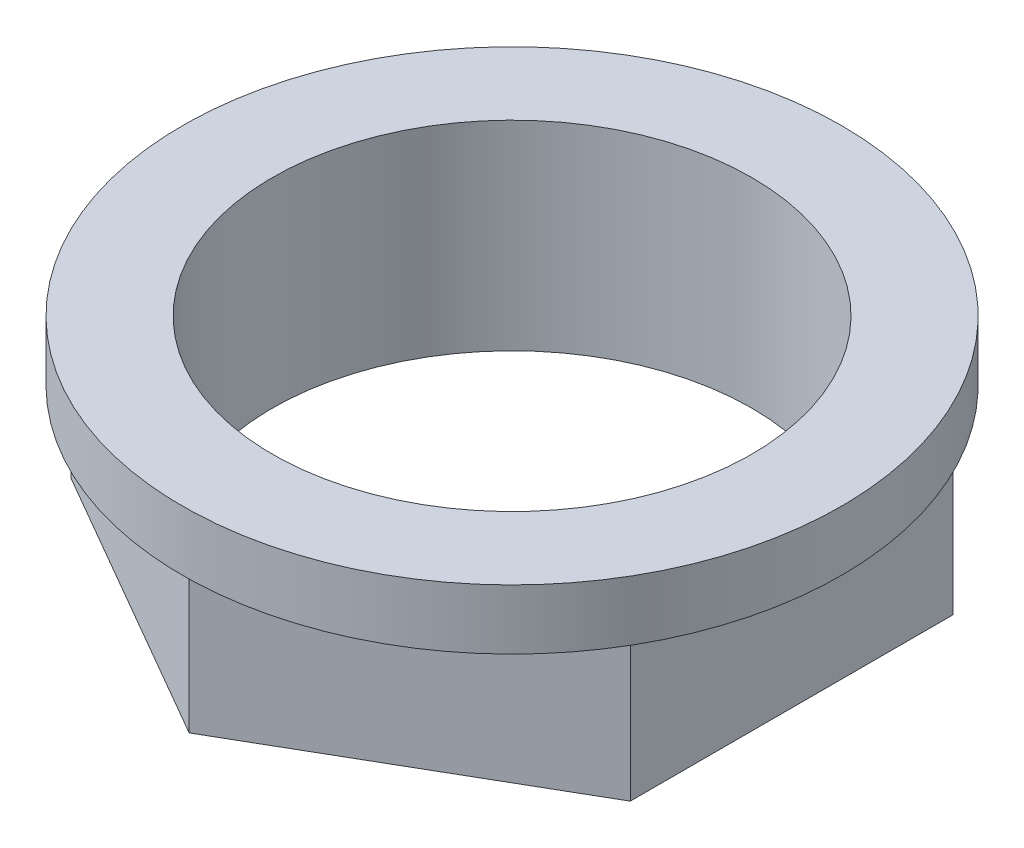
SolidWorks part; units mm, degrees
ref_plane "Спереди" through (0, 0, 0) normal (0, 0, 1) x (1, 0, 0)
ref_plane "Сверху" through (0, 0, 0) normal (0, 1, 0) x (1, 0, 0)
ref_plane "Справа" through (0, 0, 0) normal (1, 0, 0) x (0, 0, -1)
sketch "Sketch1" plane through (0, 0, 0) normal (0, 0, 1) x (1, 0, 0)
  line L0 (0, -3.4966) -> (0, 6.9158) construction
  line L2 (-8.25, 0) -> (-6, 0)
  line L3 (-8.25, 0) -> (-8.25, -5)
  line L4 (-8.25, -5) -> (-6, -5)
  line L5 (-6, 0) -> (-6, -5)
  dimension "D1" = 12
  dimension "D2" = 16.5
  dimension "D3" = 5
revolve "Revolve1" add sketch "Sketch1" angle 360 about L0
sketch "Sketch2" plane through (0, -5, 0) normal (0, -1, 0) x (1, 0, 0)
  line L1 (0, 8.0829) -> (-7, 4.0415)
  line L2 (-7, 4.0415) -> (-7, -4.0415)
  line L3 (-7, -4.0415) -> (0, -8.0829)
  line L4 (0, -8.0829) -> (7, -4.0415)
  line L5 (7, -4.0415) -> (7, 4.0415)
  line L6 (7, 4.0415) -> (0, 8.0829)
  circle A1 centre (0, 0) radius 8.25 construction
  circle A2 centre (0, 0) radius 8.25
  circle A3 centre (0, 0) radius 7 construction
  dimension "D1" = 14
extrude "Cut-Extrude1" cut sketch "Sketch2" against normal blind 3.5
